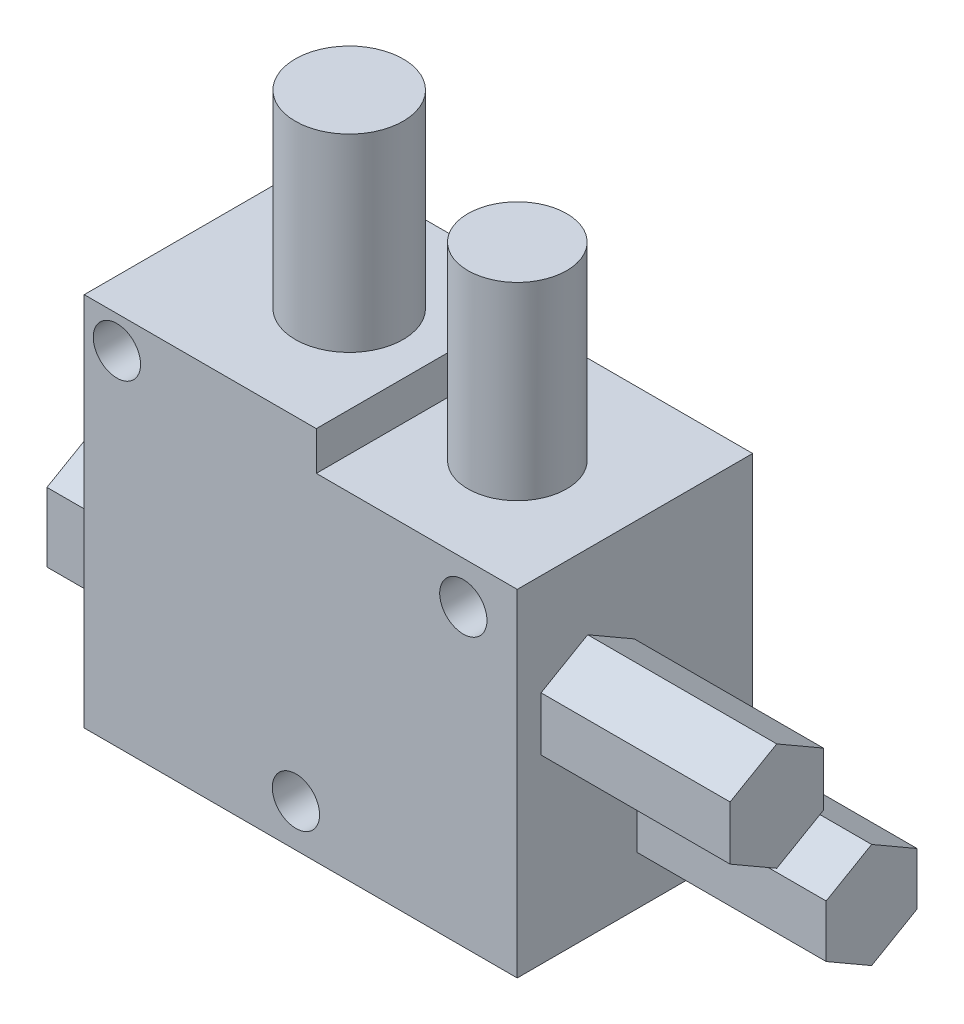
SolidWorks part; units mm, degrees
material "CA"
ref_plane "Front Plane" through (0, 0, 0) normal (0, 0, 1) x (1, 0, 0)
ref_plane "Top Plane" through (0, 0, 0) normal (0, 1, 0) x (1, 0, 0)
ref_plane "Right Plane" through (0, 0, 0) normal (1, 0, 0) x (0, 0, -1)
sketch "Sketch1" plane through (0, 0, 0) normal (0, 0, 1) x (1, 0, 0)
  line L1 (-89.6926, 53.9953) -> (-43.8926, 53.9953)
  line L2 (-89.6926, 53.9953) -> (-89.6926, 14.2953)
  line L3 (-89.6926, 14.2953) -> (-43.8926, 14.2953)
  line L4 (-43.8926, 53.9953) -> (-43.8926, 14.2953)
  dimension "D1" = 39.7
  dimension "D2" = 45.8
extrude "Boss-Extrude1" add sketch "Sketch1" along normal blind 24.9
sketch "Sketch2" plane through (0, 0, 24.9) normal (0, 0, 1) x (1, 0, 0)
  line L0 (-43.8926, 14.2953) -> (-43.8926, 53.9953) construction
  line L1 (-43.8926, 49.8953) -> (-65.1453, 49.8953)
  line L2 (-43.8926, 49.8953) -> (-43.8926, 53.9953)
  line L3 (-43.8926, 53.9953) -> (-65.1453, 53.9953)
  line L4 (-65.1453, 49.8953) -> (-65.1453, 53.9953)
  line L5 (-43.8926, 53.9953) -> (-89.6926, 53.9953) construction
  line L6 (-89.6926, 14.2953) -> (-43.8926, 14.2953) construction
  dimension "D1" = 35.6
extrude "Cut-Extrude1" cut sketch "Sketch2" against normal blind 24.9
sketch "Sketch3" plane through (0, 53.9953, 0) normal (0, 1, 0) x (1, 0, 0)
  circle A0 centre (-74.4194, -12.1449) radius 5.7079
extrude "Boss-Extrude2" add sketch "Sketch3" along normal blind 20
sketch "Sketch4" plane through (0, 49.8953, 0) normal (0, 1, 0) x (1, 0, 0)
  circle A0 centre (-55.701, -13.0819) radius 5.224
extrude "Boss-Extrude3" add sketch "Sketch4" along normal blind 20
sketch "Sketch5" plane through (-89.6926, 0, 0) normal (-1, 0, 0) x (0, 0, 1)
  line L1 (18.846, 21.013) -> (18.846, 28.3135)
  line L2 (18.846, 28.3135) -> (12.5235, 31.9638)
  line L3 (12.5235, 31.9638) -> (6.2011, 28.3135)
  line L4 (6.2011, 28.3135) -> (6.2011, 21.013)
  line L5 (6.2011, 21.013) -> (12.5235, 17.3627)
  line L6 (12.5235, 17.3627) -> (18.846, 21.013)
  circle A0 centre (12.5235, 24.6633) radius 6.3225 construction
extrude "Boss-Extrude4" add sketch "Sketch5" along normal blind 10
sketch "Sketch6" plane through (-43.8926, 0, 0) normal (1, 0, 0) x (0, 0, -1)
  line L1 (-17.4492, 30.6181) -> (-12.5149, 33.4669)
  line L2 (-12.5149, 33.4669) -> (-12.5149, 39.1645)
  line L3 (-12.5149, 39.1645) -> (-17.4492, 42.0133)
  line L4 (-17.4492, 42.0133) -> (-22.3834, 39.1645)
  line L5 (-22.3834, 39.1645) -> (-22.3834, 33.4669)
  line L6 (-22.3834, 33.4669) -> (-17.4492, 30.6181)
  line L7 (-7.4141, 16.6867) -> (-2.6072, 19.4619)
  line L8 (-2.6072, 19.4619) -> (-2.6072, 25.0125)
  line L9 (-2.6072, 25.0125) -> (-7.4141, 27.7877)
  line L10 (-7.4141, 27.7877) -> (-12.221, 25.0125)
  line L11 (-12.221, 25.0125) -> (-12.221, 19.4619)
  line L12 (-12.221, 19.4619) -> (-7.4141, 16.6867)
  circle A0 centre (-17.4492, 36.3157) radius 4.9342 construction
  circle A1 centre (-7.4141, 22.2372) radius 4.8069 construction
extrude "Boss-Extrude5" add sketch "Sketch6" along normal blind 20
sketch "Sketch7" plane through (0, 0, 24.9) normal (0, 0, 1) x (1, 0, 0)
  circle A0 centre (-67.3008, 18.7909) radius 2.5
  circle A1 centre (-86.237, 50.578) radius 2.5
  circle A2 centre (-49.5946, 45.446) radius 2.5
  dimension "D1" = 37
  dimension "D2" = 37
  dimension "D3" = 32
extrude "Cut-Extrude2" cut sketch "Sketch7" against normal blind 100
